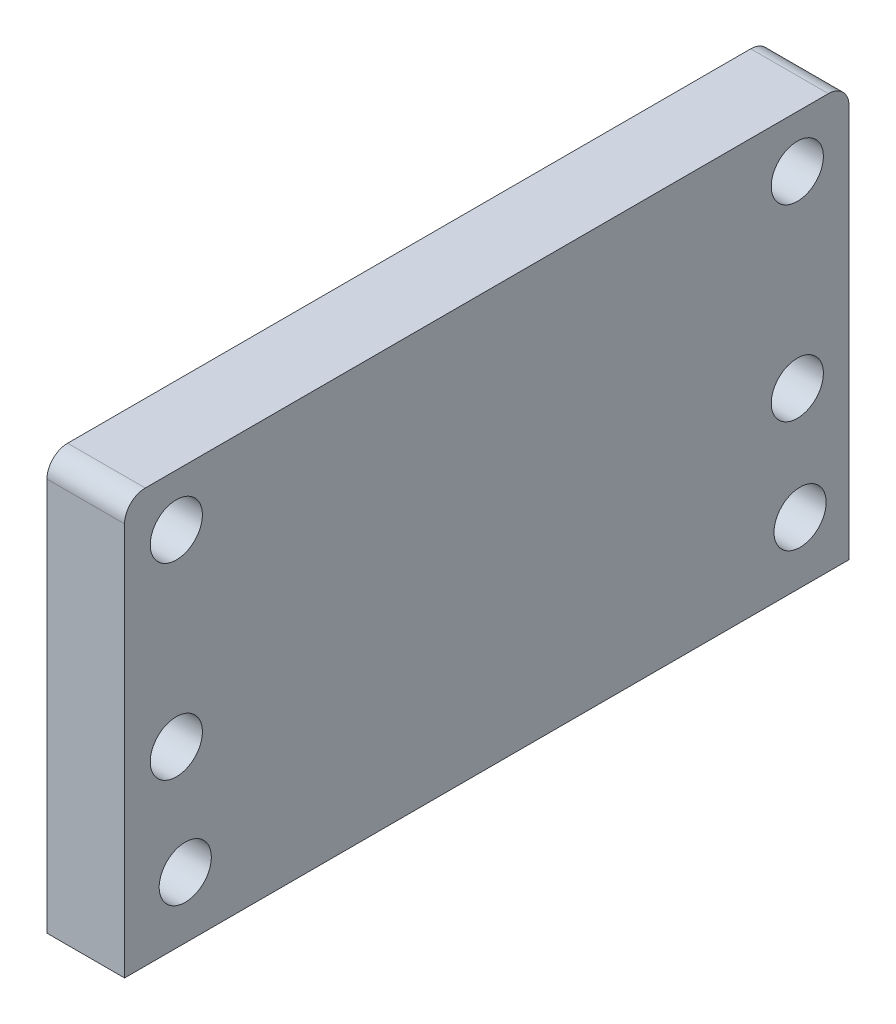
SolidWorks part; units mm, degrees
ref_plane "Front Plane" through (0, 0, 0) normal (0, 0, 1) x (1, 0, 0)
ref_plane "Top Plane" through (0, 0, 0) normal (0, 1, 0) x (1, 0, 0)
ref_plane "Right Plane" through (0, 0, 0) normal (1, 0, 0) x (0, 0, -1)
sketch "Sketch1" plane through (0, 0, 0) normal (1, 0, 0) x (0, 0, -1)
  line L1 (44.45, -25.4) -> (-44.45, -25.4)
  line L2 (44.45, -25.4) -> (44.45, 25.4)
  line L3 (44.45, 25.4) -> (-44.45, 25.4)
  line L4 (-44.45, -25.4) -> (-44.45, 25.4)
  line L5 (44.45, -25.4) -> (-44.45, 25.4) construction
  line L6 (44.45, 25.4) -> (-44.45, -25.4) construction
  point P0 (0, 0)
  dimension "D1" = 88.9
  dimension "D2" = 50.8
extrude "Boss-Extrude1" add sketch "Sketch1" along normal mid plane 9.525
sketch "Sketch2" plane through (4.7625, 0, 0) normal (1, 0, 0) x (0, 0, -1)
  line L0 (44.45, 25.4) -> (-44.45, 25.4) construction
  line L3 (-44.45, 25.4) -> (-44.45, -25.4) construction
  line L4 (44.45, -25.4) -> (44.45, 25.4) construction
  circle A0 centre (-38.1, 19.05) radius 3.2
  circle A1 centre (38.1, 19.05) radius 3.2
  circle A2 centre (-38.1, -4) radius 3.2
  circle A3 centre (38.1, -4) radius 3.2
  dimension "D1" = 6.4
  dimension "D2" = 6.35
  dimension "D3" = 76.2
  dimension "D4" = 6.4
  dimension "D5" = 6.35
  dimension "D6" = 6.4
  dimension "D7" = 6.4
  dimension "D10" = 6.35
  dimension "D11" = 6.35
  dimension "D12" = 6.35
  dimension "D8" = 23.05
  dimension "D9" = 23.05
extrude "Cut-Extrude1" cut sketch "Sketch2" against normal through all
fillet "Fillet3" radius 2.54 1 edges at (0, 25.4, 44.45)
fillet "Fillet4" radius 2.54 1 edges at (0, 25.4, -44.45)
sketch "Sketch4" plane through (4.7625, 0, 0) normal (1, 0, 0) x (0, 0, -1)
  circle A0 centre (-37.0021, -17.8793) radius 3.2
  circle A1 centre (38.4403, -17.8793) radius 3.2
  dimension "D1" = 6.4
  dimension "D2" = 6.4
extrude "Cut-Extrude5" cut sketch "Sketch4" against normal through all
